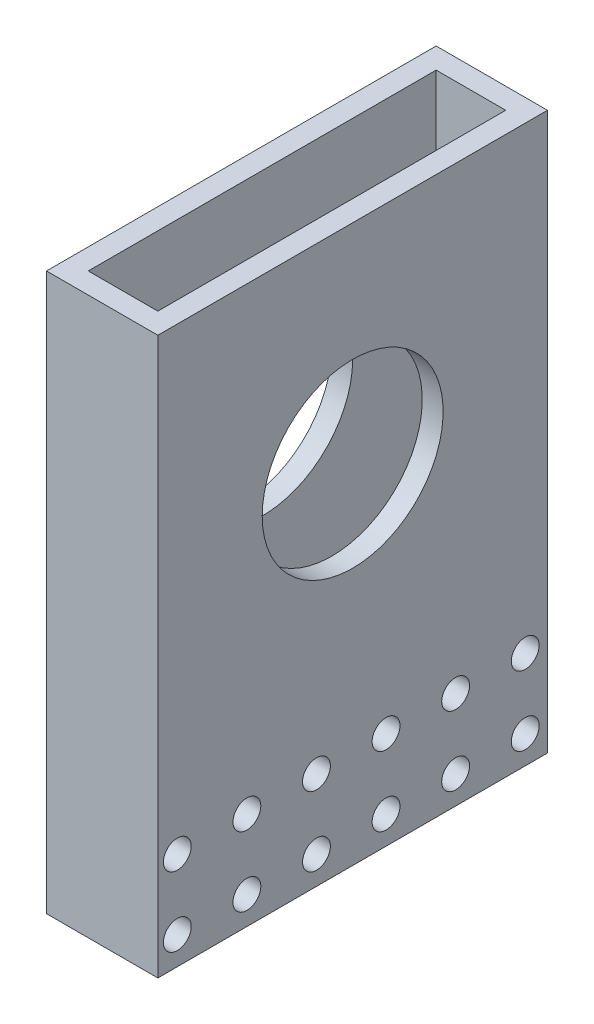
SolidWorks part; units mm, degrees
ref_plane "Front Plane" through (0, 0, 0) normal (0, 0, 1) x (1, 0, 0)
ref_plane "Top Plane" through (0, 0, 0) normal (0, 1, 0) x (1, 0, 0)
ref_plane "Right Plane" through (0, 0, 0) normal (1, 0, 0) x (0, 0, -1)
sketch "Sketch1" plane through (0, 0, 0) normal (0, 1, 0) x (1, 0, 0)
  line L1 (-5, 25) -> (5, 25)
  line L2 (-5, 25) -> (-5, -25)
  line L3 (-5, -25) -> (5, -25)
  line L4 (5, 25) -> (5, -25)
  line L5 (-5, 25) -> (5, -25) construction
  line L6 (-5, -25) -> (5, 25) construction
  point P0 (0, 0)
  dimension "D1" = 10
  dimension "D2" = 50
extrude "Extrude-Thin1" add sketch "Sketch1" along normal blind 80 thin thin type one direction wall 3
sketch "Sketch2" plane through (-8, 0, 0) normal (-1, 0, 0) x (0, 0, 1)
  circle A0 centre (0, 50) radius 13
  circle A1 centre (-24.7974, 4.0155) radius 2
  circle A2 centre (-14.7974, 4.0155) radius 2
  circle A3 centre (-4.7974, 4.0155) radius 2
  circle A4 centre (5.2026, 4.0155) radius 2
  circle A5 centre (15.2026, 4.0155) radius 2
  circle A6 centre (25.2026, 4.0155) radius 2
  circle A7 centre (-14.7974, 14.0155) radius 2
  circle A8 centre (-4.7974, 14.0155) radius 2
  circle A9 centre (5.2026, 14.0155) radius 2
  circle A10 centre (15.2026, 14.0155) radius 2
  circle A11 centre (25.2026, 14.0155) radius 2
  circle A12 centre (-24.7974, 14.0155) radius 2
  point P5 (-24.7974, 4.0155)
  dimension "D1" = 50
  dimension "D2" = 26
  dimension "D3" = 6
  dimension "D4" = 2
extrude "Cut-Extrude1" cut sketch "Sketch2" against normal through all
